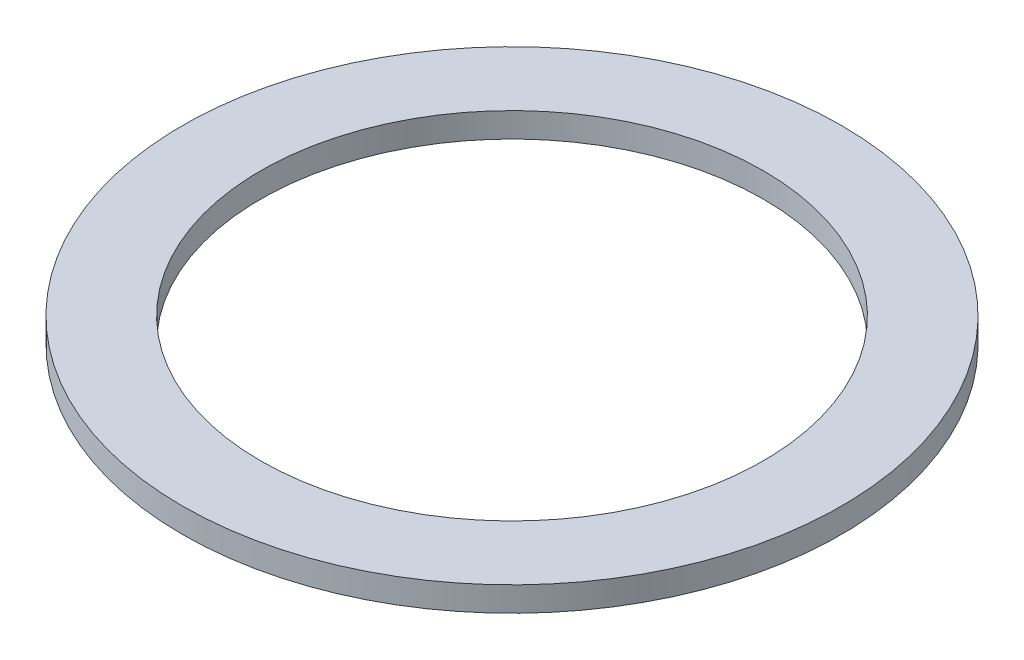
SolidWorks part; units mm, degrees
ref_plane "Front" through (0, 0, 0) normal (0, 0, 1) x (1, 0, 0)
ref_plane "Top" through (0, 0, 0) normal (0, 1, 0) x (1, 0, 0)
ref_plane "Right" through (0, 0, 0) normal (1, 0, 0) x (0, 0, -1)
sketch "Sketch1" plane through (0, 0, 0) normal (0, 1, 0) x (1, 0, 0)
  circle A0 centre (0, 0) radius 6.7945
  circle A1 centre (0, 0) radius 5.1816
  dimension "D1" = 10.3632
  dimension "D2" = 13.589
extrude "Boss-Extrude1" add sketch "Sketch1" along normal blind 0.508
